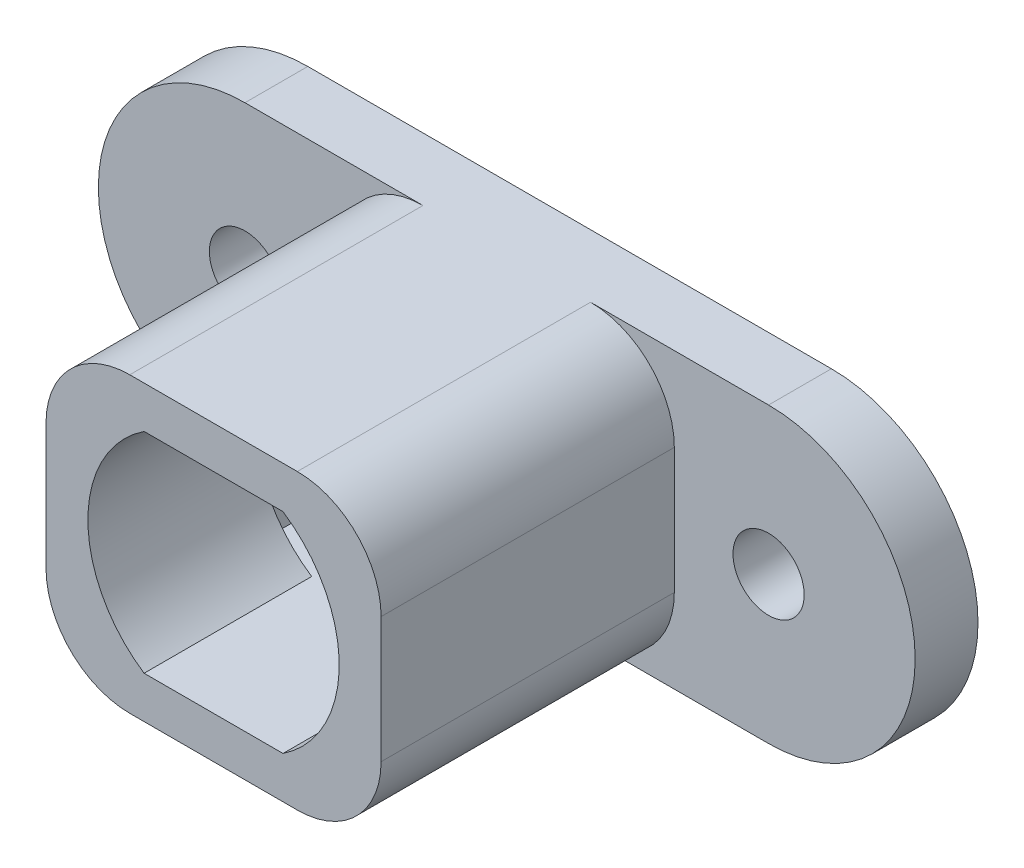
SolidWorks part; units mm, degrees
material "ABS"
ref_plane "Front Plane" through (0, 0, 0) normal (0, 0, 1) x (1, 0, 0)
ref_plane "Top Plane" through (0, 0, 0) normal (0, 1, 0) x (1, 0, 0)
ref_plane "Right Plane" through (0, 0, 0) normal (1, 0, 0) x (0, 0, -1)
sketch "Sketch1" plane through (0, 0, 0) normal (0, 0, 1) x (1, 0, 0)
  line L0 (0, 7) -> (0, -7) construction
  line L1 (-12.5, 7) -> (12.5, 7)
  line L2 (-12.5, 7) -> (-12.5, -7) construction
  line L3 (-12.5, -7) -> (12.5, -7)
  line L4 (12.5, 7) -> (12.5, -7) construction
  line L5 (-12.5, 7) -> (12.5, -7) construction
  line L6 (-12.5, -7) -> (12.5, 7) construction
  line L8 (-6, 5) -> (6, 5)
  line L9 (-6, 5) -> (-6, -5)
  line L10 (-6, -5) -> (6, -5)
  line L11 (6, 5) -> (6, -5)
  line L12 (-6, 5) -> (6, -5) construction
  line L13 (-6, -5) -> (6, 5) construction
  arc A0 (-12.5, 7) -> (-12.5, -7) centre (-12.5, 0) ccw
  arc A1 (12.5, 7) -> (12.5, -7) centre (12.5, 0) cw
  point P0 (0, 0)
  point P3 (0, 0)
  dimension "D1" = 25
  dimension "D2" = 14
  dimension "D3" = 12
  dimension "D4" = 10
extrude "Boss-Extrude3" add sketch "Sketch1" along normal blind 3 contours A0 L3 A1 L1
sketch "Sketch4" plane through (0, 0, 3) normal (0, 0, 1) x (1, 0, 0)
  line L0 (-6, -5) -> (6, -5) construction
  line L1 (6, -5) -> (6, 5) construction
  line L2 (-6, 5) -> (-6, -5) construction
  line L3 (6, 5) -> (-6, 5) construction
  line L4 (-6, -5) -> (6, -5)
  line L5 (6, -5) -> (6, 5)
  line L6 (-6, 5) -> (-6, -5)
  line L7 (6, 5) -> (-6, 5)
  line L8 (-12.5, -7) -> (12.5, -7) construction
  line L9 (-8, 7) -> (8, 7)
  line L10 (-8, 7) -> (-8, -7)
  line L11 (-8, -7) -> (8, -7)
  line L12 (8, 7) -> (8, -7)
  line L13 (-8, 7) -> (8, -7) construction
  line L14 (-8, -7) -> (8, 7) construction
  point P2 (0, 0)
  dimension "D1" = 2
extrude "Boss-Extrude4" add sketch "Sketch4" along normal offset from surface (6 mm away) 9 up to face at (0, 0, 0)
sketch "Sketch5" plane through (0, 0, 9) normal (0, 0, 1) x (1, 0, 0)
  line L0 (6, -5) -> (-6, -5) construction
  line L1 (-6, 5) -> (6, 5) construction
  line L2 (0, 0) -> (0, 5) construction
  line L3 (3.3166, 5) -> (-3.3166, 5)
  line L4 (8, 7) -> (-8, 7)
  line L5 (-8, 7) -> (-8, -7)
  line L6 (-8, -7) -> (8, -7)
  line L7 (8, -7) -> (8, 7)
  line L8 (8, 7) -> (-8, 7)
  line L9 (-8, 7) -> (-8, -7)
  line L10 (-8, -7) -> (8, -7)
  line L11 (8, -7) -> (8, 7)
  line L12 (0, 0) -> (-6, 0) construction
  line L13 (3.3166, -5) -> (-3.3166, -5)
  circle A0 centre (0, 0) radius 6 construction
  arc A1 (-3.3166, -5) -> (-3.3166, 5) centre (0, 0) cw
  arc A2 (3.3166, -5) -> (3.3166, 5) centre (0, 0) ccw
  point P18 (0, -5)
  dimension "D1" = 12
  dimension "D2" = 0
extrude "Boss-Extrude5" add sketch "Sketch5" along normal blind 8
hole_wizard "M3 Clearance Hole1" positions "Sketch6" profile "Sketch7" hole size "M3" standard "ISO"
sketch "Sketch6" plane through (0, 0, 3) normal (0, 0, 1) x (1, 0, 0)
  point P0 (-12.5, 0)
  point P3 (12.5, 0)
sketch "Sketch7" plane through (-12.5, 0, 3) normal (1, 0, 0) x (0, -1, 0)
  line L0 (0, 0) -> (0, 13.0215)
  line L1 (0, 13.0215) -> (1.7, 12)
  line L2 (1.7, 12) -> (1.7, 0)
  line L5 (1.7, 0) -> (0, 0)
  line L10 (0, 13.0215) -> (-1.7, 12) construction
  line L11 (0, -6.35) -> (0, 107.95) construction
  dimension "Hole Dia." = 3.4
  dimension "Hole Depth" = 12
  dimension "Drill Angle" = 118
fillet "Fillet1" radius 4 4 edges at (8, -7, 10) (-8, -7, 10) (8, 7, 10) (-8, 7, 10)
